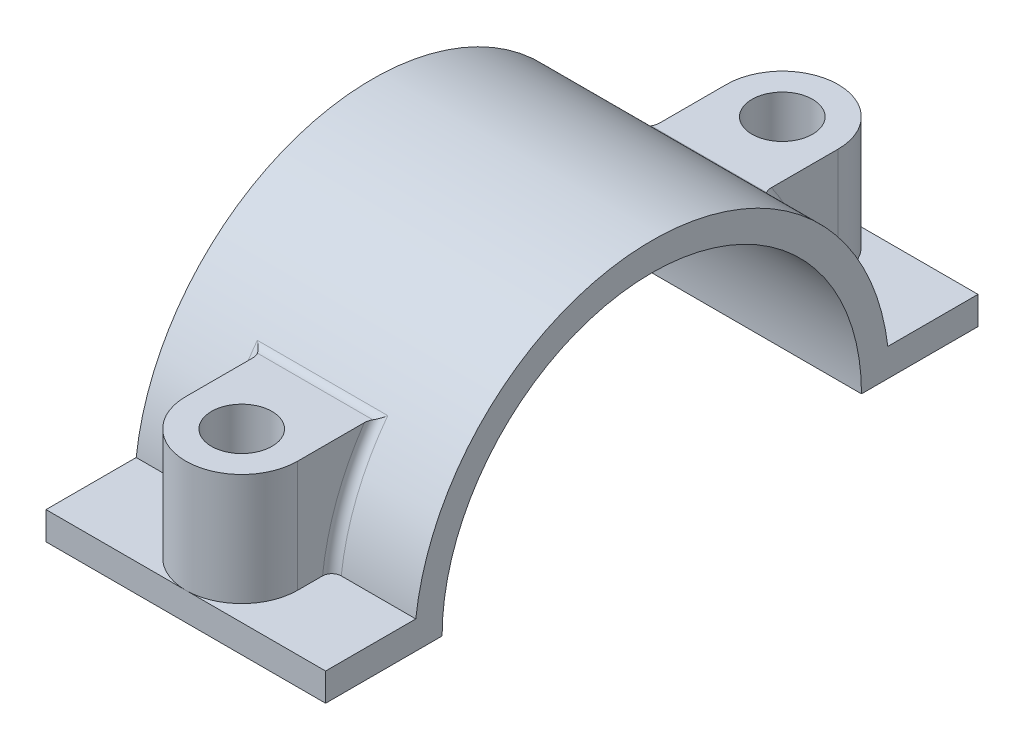
SolidWorks part; units mm, degrees
ref_plane "Front Plane" through (0, 0, 0) normal (0, 0, 1) x (1, 0, 0)
ref_plane "Top Plane" through (0, 0, 0) normal (0, 1, 0) x (1, 0, 0)
ref_plane "Right Plane" through (0, 0, 0) normal (1, 0, 0) x (0, 0, -1)
sketch "Sketch1" plane through (0, 0, 0) normal (1, 0, 0) x (0, 0, -1)
  line L0 (-22.5, 0) -> (-35, 0)
  line L1 (0, 0) -> (0, 33.3302) construction
  line L2 (22.5, 0) -> (35, 0)
  line L3 (25.3229, 3) -> (35, 3)
  line L4 (-25.3229, 3) -> (-35, 3)
  line L5 (-35, 0) -> (-35, 3)
  line L6 (35, 3) -> (35, 0)
  arc A0 (22.5, 0) -> (-22.5, 0) centre (0, 0) ccw
  arc A1 (25.3229, 3) -> (-25.3229, 3) centre (0, 0) ccw
  dimension "D1" = 45
  dimension "D2" = 35
  dimension "D3" = 3
extrude "Boss-Extrude1" add sketch "Sketch1" along normal mid plane 30
ref_plane "Plane1" through (0, 15, 0) normal (0, 1, 0) x (1, 0, 0)
sketch "Sketch2" plane through (0, 15, 0) normal (0, 1, 0) x (1, 0, 0)
  line L0 (0, 0) -> (0, -39.1975) construction
  line L1 (15, -35) -> (-15, -35) construction
  line L2 (-6, -29) -> (-6, -19)
  line L3 (-6, -19) -> (6, -19)
  line L4 (6, -19) -> (6, -29)
  arc A0 (-6, -29) -> (6, -29) centre (0, -29) ccw
  dimension "D1" = 12
  dimension "D2" = 10
extrude "Boss-Extrude2" add sketch "Sketch2" against normal up to body
sketch "Sketch3" plane through (0, 15, 0) normal (0, 1, 0) x (1, 0, 0)
  circle A0 centre (0, -29) radius 3.25
  dimension "D1" = 6.5
extrude "Cut-Extrude1" cut sketch "Sketch3" against normal through all
mirror "Mirror1" about plane through (0, 0, 0) normal (0, 0, 1) of "Cut-Extrude1", "Boss-Extrude2"
fillet "Fillet1" radius 1 6 edges at (-6, 9.3019, 23.7429) (0, 15, 20.6216) (6, 9.3019, 23.7429) (-6, 9.3019, -23.7429) (6, 9.3019, -23.7429) (0, 15, -20.6216)
